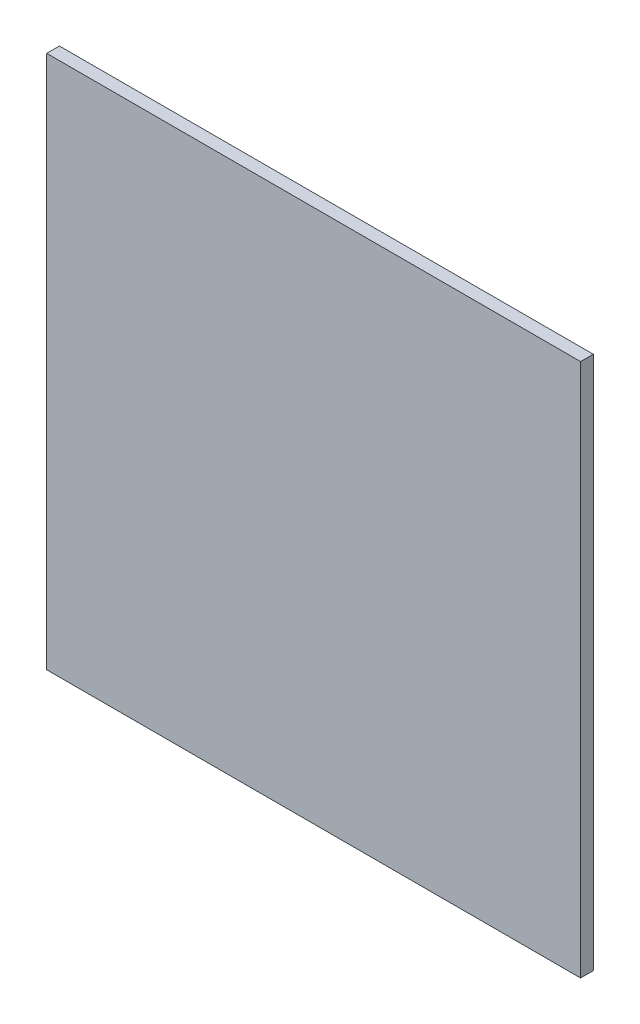
SolidWorks part; units mm, degrees
ref_plane "Front Plane" through (0, 0, 0) normal (0, 0, 1) x (1, 0, 0)
ref_plane "Top Plane" through (0, 0, 0) normal (0, 1, 0) x (1, 0, 0)
ref_plane "Right Plane" through (0, 0, 0) normal (1, 0, 0) x (0, 0, -1)
sketch "Sketch1" plane through (0, 0, 0) normal (0, 0, 1) x (1, 0, 0)
  line L1 (53.34, 53.34) -> (-53.34, 53.34)
  line L2 (53.34, 53.34) -> (53.34, -53.34)
  line L3 (53.34, -53.34) -> (-53.34, -53.34)
  line L4 (-53.34, 53.34) -> (-53.34, -53.34)
  line L5 (53.34, 53.34) -> (-53.34, -53.34) construction
  line L6 (53.34, -53.34) -> (-53.34, 53.34) construction
  point P0 (0, 0)
  dimension "D1" = 106.68
  dimension "D2" = 106.68
extrude "Boss-Extrude1" add sketch "Sketch1" along normal blind 2.54
